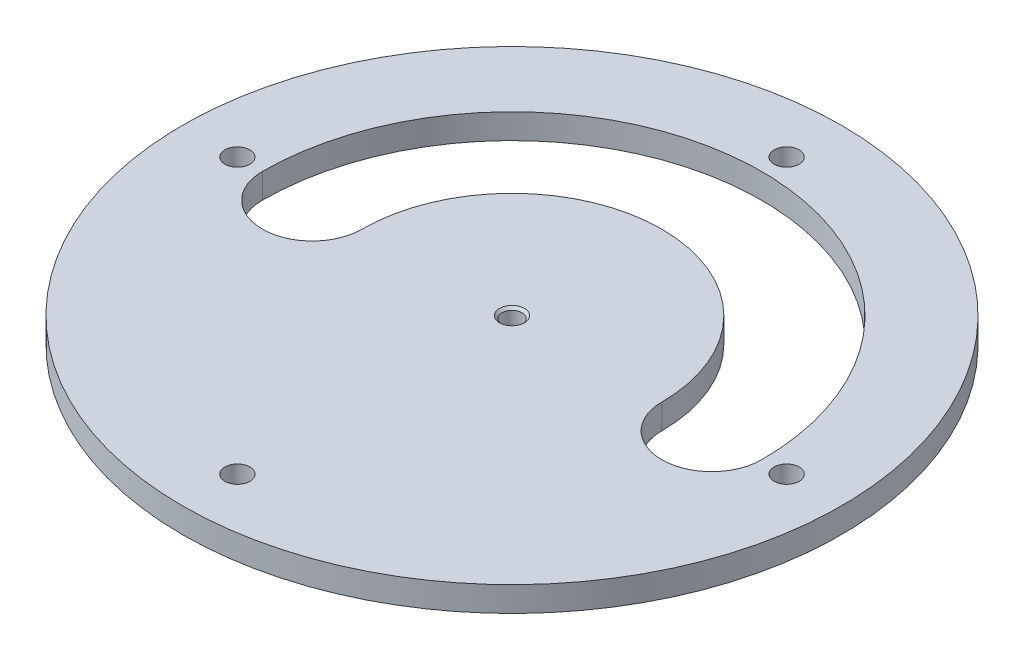
SolidWorks part; units mm, degrees
ref_plane "Front Plane" through (0, 0, 0) normal (0, 0, 1) x (1, 0, 0)
ref_plane "Top Plane" through (0, 0, 0) normal (0, 1, 0) x (1, 0, 0)
ref_plane "Right Plane" through (0, 0, 0) normal (1, 0, 0) x (0, 0, -1)
sketch "Sketch1" plane through (0, 0, 0) normal (0, 1, 0) x (1, 0, 0)
  line L0 (0, 45.2247) -> (0, -45.2247) construction
  circle A0 centre (0, 0) radius 33
  circle A1 centre (0, 0) radius 27.5 construction
  circle A2 centre (0, 27.5) radius 1.25
  circle A3 centre (27.5, 0) radius 1.25
  circle A4 centre (0, -27.5) radius 1.25
  circle A5 centre (-27.5, 0) radius 1.25
  circle A6 centre (0, 0) radius 1
  point P16 (0, 0)
  dimension "D1" = 66
  dimension "D2" = 55
  dimension "D3" = 2.5
  dimension "D5" = 2
  dimension "D4" = 4
extrude "Boss-Extrude2" add sketch "Sketch1" along normal blind 2.5 contours A0 | A5 | A2 | A3 | A4 | A6
sketch "Sketch2" plane through (0, 0, 0) normal (0, 1, 0) x (1, 0, 0)
  line L0 (-61.2096, 0) -> (61.2096, 0) construction
  line L1 (0, 40.3423) -> (0, -40.3423) construction
  arc A0 (25, 0) -> (-25, 0) centre (0, 0) ccw
  circle A1 centre (0, 0) radius 20 construction
  arc A2 (15, 0) -> (-15, 0) centre (0, 0) ccw
  arc A3 (15, 0) -> (25, 0) centre (20, 0) ccw
  arc A4 (-15, 0) -> (-25, 0) centre (-20, 0) cw
  point P8 (0, 0)
  point P11 (0, 0)
  dimension "D1" = 50
  dimension "D2" = 40
extrude "Cut-Extrude1" cut sketch "Sketch2" against normal blind 10 and the other way through all
chamfer "Chamfer5" distance 0.25 angle 45 1 edges at (0, 2.5, 1)
